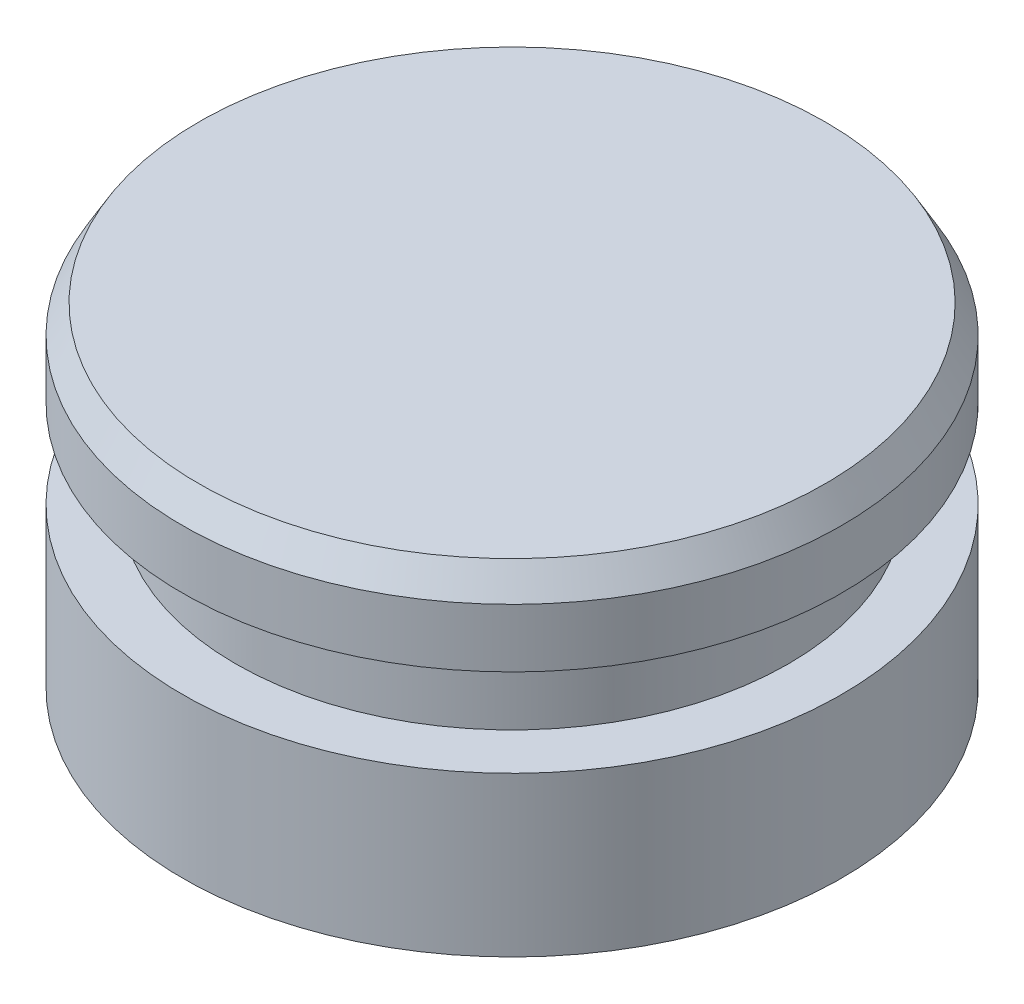
SolidWorks part; units mm, degrees
ref_plane "Front Plane" through (0, 0, 0) normal (0, 0, 1) x (1, 0, 0)
ref_plane "Top Plane" through (0, 0, 0) normal (0, 1, 0) x (1, 0, 0)
ref_plane "Right Plane" through (0, 0, 0) normal (1, 0, 0) x (0, 0, -1)
sketch "Sketch1" plane through (0, 0, 0) normal (0, 0, 1) x (1, 0, 0)
  line L0 (0, 0) -> (0, 9.652) construction
  line L1 (0, 0) -> (-9.5377, 0)
  line L4 (-8.001, 4.6037) -> (-8.001, 7.1437)
  line L5 (-8.001, 7.1437) -> (-9.5377, 7.1437)
  line L6 (-9.5377, 7.1437) -> (-9.5377, 9.652)
  line L7 (-9.5377, 9.652) -> (0, 9.652)
  line L9 (0, 0) -> (0, 9.652)
  line L11 (-8.001, 4.6037) -> (-9.5377, 4.6037)
  line L12 (-9.5377, 4.6037) -> (-9.5377, 0)
  dimension "D1" = 9.652
  dimension "D2" = 9.5377
  dimension "D3" = 2.54
  dimension "D6" = 8.001
  dimension "D7" = 7.1437
revolve "Revolve1" add sketch "Sketch1" angle 360 about L9
chamfer "Chamfer1" distance 0.4704 angle 60 1 edges at (0, 9.652, -9.5377)
